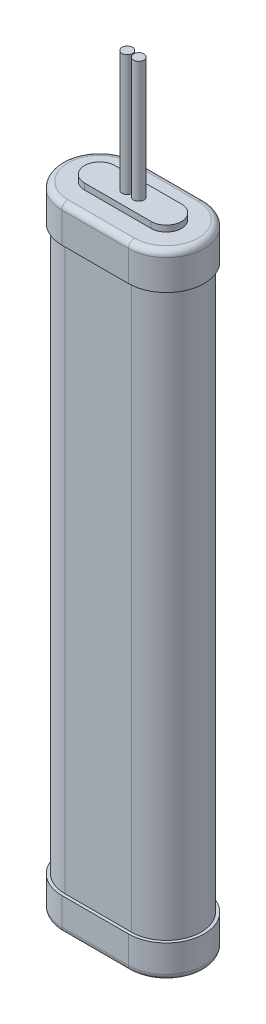
SolidWorks part; units mm, degrees
ref_plane "Face" through (0, 0, 0) normal (0, 0, 1) x (1, 0, 0)
ref_plane "Dessus" through (0, 0, 0) normal (0, 1, 0) x (1, 0, 0)
ref_plane "Droite" through (0, 0, 0) normal (1, 0, 0) x (0, 0, -1)
sketch "Esquisse1" plane through (0, 0, 0) normal (0, 1, 0) x (1, 0, 0)
  line L0 (0, 0) -> (22, 0)
  line L1 (0, 25) -> (22, 25)
  arc A0 (0, 0) -> (0, 25) centre (0, 12.5) cw
  arc A1 (22, 0) -> (22, 25) centre (22, 12.5) ccw
  dimension "D1" = 12.5
  dimension "D2" = 22
extrude "Extrusion1" add sketch "Esquisse1" along normal blind 11
sketch "Esquisse3" plane through (0, 11, 0) normal (0, 1, 0) x (1, 0, 0)
  line L0 (0, 25) -> (0, 0) construction
  line L1 (22, 25) -> (22, 0) construction
  line L2 (-12.5, 12.5) -> (34.5, 12.5) construction
  line L3 (0, 1) -> (22, 1)
  line L4 (0, 24) -> (22, 24)
  arc A0 (0, 25) -> (0, 0) centre (0, 12.5) ccw construction
  arc A1 (22, 0) -> (22, 25) centre (22, 12.5) ccw construction
  arc A2 (0, 1) -> (0, 24) centre (0, 12.5) cw
  arc A3 (22, 1) -> (22, 24) centre (22, 12.5) ccw
  dimension "D1" = 11.5
extrude "Extrusion3" add sketch "Esquisse3" along normal blind 186
sketch "Esquisse4" plane through (0, 197, 0) normal (0, 1, 0) x (1, 0, 0)
  line L0 (0, 25) -> (22, 25)
  line L1 (0, 0) -> (22, 0)
  arc A0 (0, 25) -> (0, 0) centre (0, 12.5) ccw
  arc A1 (22, 25) -> (22, 0) centre (22, 12.5) cw
extrude "Extrusion4" add sketch "Esquisse4" along normal blind 12
sketch "Esquisse5" plane through (0, 209, 0) normal (0, 1, 0) x (1, 0, 0)
  line L0 (0, 25) -> (0, 0) construction
  line L1 (22, 25) -> (22, 0) construction
  line L2 (0, 0) -> (22, 0) construction
  line L3 (-12.5, 12.5) -> (34.5, 12.5) construction
  line L4 (0, 17.5) -> (22, 17.5)
  line L5 (0, 7.5) -> (22, 7.5)
  arc A0 (22, 0) -> (22, 25) centre (22, 12.5) ccw construction
  arc A1 (0, 25) -> (0, 0) centre (0, 12.5) ccw construction
  arc A2 (0, 17.5) -> (0, 7.5) centre (0, 12.5) ccw
  arc A3 (22, 17.5) -> (22, 7.5) centre (22, 12.5) cw
  dimension "D1" = 5
extrude "Extrusion5" add sketch "Esquisse5" along normal blind 2
fillet "Congé1" radius 2 8 edges at (11, 0, 0) (34.5, 0, -12.5) (11, 0, -25) (-12.5, 0, -12.5) (34.5, 209, -12.5) (11, 209, 0) (11, 209, -25) (-12.5, 209, -12.5)
sketch "Esquisse6" plane through (0, 211, 0) normal (0, 1, 0) x (1, 0, 0)
  line L0 (-5, 12.5) -> (27, 12.5) construction
  line L1 (11, 17.5) -> (11, 7.5) construction
  line L3 (22, 17.5) -> (0, 17.5) construction
  line L4 (0, 7.5) -> (22, 7.5) construction
  arc A0 (0, 17.5) -> (0, 7.5) centre (0, 12.5) ccw construction
  arc A1 (22, 7.5) -> (22, 17.5) centre (22, 12.5) ccw construction
  circle A2 centre (9.1, 12.5) radius 1.75
  circle A3 centre (12.9, 12.5) radius 1.75
  dimension "D1" = 3.5
  dimension "D2" = 1.9
extrude "Extrusion6" add sketch "Esquisse6" along normal blind 40
